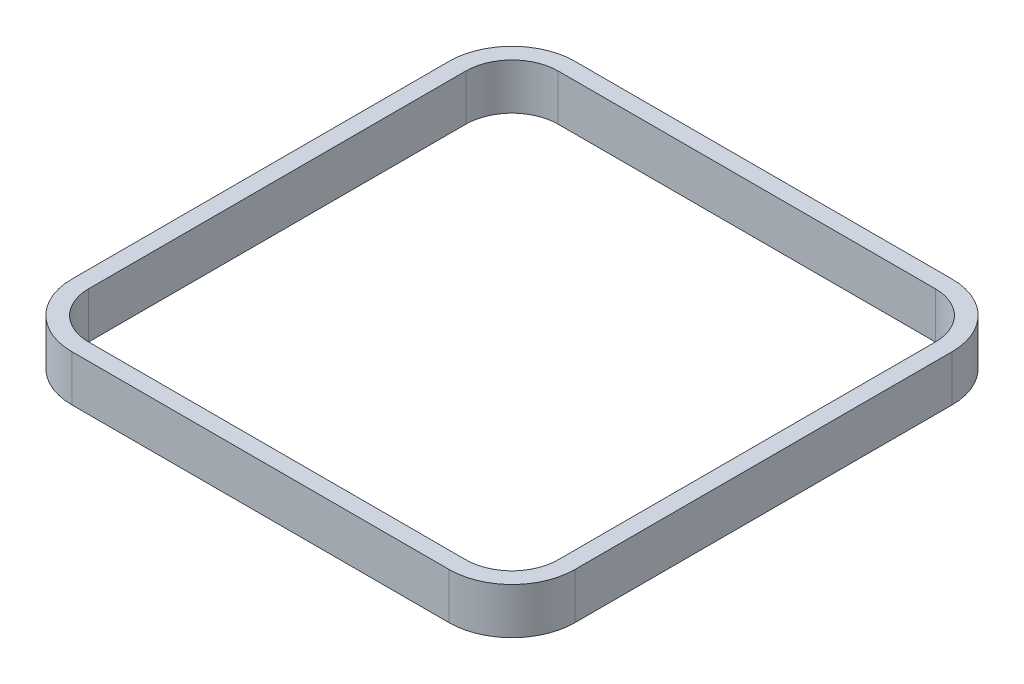
SolidWorks part; units mm, degrees
ref_plane "Front Plane" through (0, 0, 0) normal (0, 0, 1) x (1, 0, 0)
ref_plane "Top Plane" through (0, 0, 0) normal (0, 1, 0) x (1, 0, 0)
ref_plane "Right Plane" through (0, 0, 0) normal (1, 0, 0) x (0, 0, -1)
sketch "Sketch1" plane through (0, 0, 0) normal (0, 1, 0) x (1, 0, 0)
  line L1 (-450, -600) -> (450, -600)
  line L2 (-600, -450) -> (-600, 450)
  line L3 (-450, 600) -> (450, 600)
  line L4 (600, -450) -> (600, 450)
  line L5 (-600, -600) -> (600, 600) construction
  line L6 (-600, 600) -> (600, -600) construction
  arc A0 (450, 600) -> (600, 450) centre (450, 450) cw
  arc A1 (600, -450) -> (450, -600) centre (450, -450) cw
  arc A2 (-450, -600) -> (-600, -450) centre (-450, -450) cw
  arc A3 (-600, 450) -> (-450, 600) centre (-450, 450) cw
  point P0 (0, 0)
  dimension "D3" = 150
  dimension "D1" = 1200
  dimension "D2" = 1200
extrude "Boss-Extrude1" add sketch "Sketch1" along normal blind 150
sketch "Sketch2" plane through (0, 150, 0) normal (0, 1, 0) x (1, 0, 0)
  line L8 (450, 560) -> (-450, 560)
  line L9 (-560, 450) -> (-560, -450)
  line L10 (-450, -560) -> (450, -560)
  line L11 (560, -450) -> (560, 450)
  line L12 (450, 560) -> (-450, 560)
  line L13 (-560, 450) -> (-560, -450)
  line L14 (-450, -560) -> (450, -560)
  line L15 (560, -450) -> (560, 450)
  arc A8 (560, 450) -> (450, 560) centre (450, 450) ccw
  arc A9 (-450, 560) -> (-560, 450) centre (-450, 450) ccw
  arc A10 (-560, -450) -> (-450, -560) centre (-450, -450) ccw
  arc A11 (450, -560) -> (560, -450) centre (450, -450) ccw
  arc A12 (560, 450) -> (450, 560) centre (450, 450) ccw
  arc A13 (-450, 560) -> (-560, 450) centre (-450, 450) ccw
  arc A14 (-560, -450) -> (-450, -560) centre (-450, -450) ccw
  arc A15 (450, -560) -> (560, -450) centre (450, -450) ccw
  dimension "D1" = 40
extrude "Cut-Extrude1" cut sketch "Sketch2" against normal blind 110
sketch "Sketch3" plane through (0, 40, 0) normal (0, 1, 0) x (1, 0, 0)
  circle A0 centre (249.3488, 217.5584) radius 52.0745
extrude "Cut-Extrude2" cut sketch "Sketch3" against normal blind 110
sketch "Sketch4" plane through (0, 40, 0) normal (0, 1, 0) x (1, 0, 0)
  line L0 (450, 600) -> (-450, 600) construction
  line L1 (-600, 450) -> (-600, -450) construction
  circle A0 centre (-450, 450) radius 90
  circle A1 centre (450, 450) radius 90
  circle A2 centre (450, -450) radius 90
  circle A3 centre (-450, -450) radius 90
  dimension "D1" = 180
  dimension "D2" = 150
  dimension "D3" = 150
  dimension "D4" = 180
  dimension "D5" = 180
  dimension "D6" = 180
sketch "Sketch5" plane through (0, 40, 0) normal (0, 1, 0) x (1, 0, 0)
  circle A0 centre (0, 0) radius 472.5
  dimension "D1" = 945
sketch "Sketch7" plane through (0, 0, 0) normal (0, -1, 0) x (1, 0, 0)
  line L8 (600, -450) -> (600, 450)
  line L9 (450, 600) -> (-450, 600)
  line L10 (-600, 450) -> (-600, -450)
  line L11 (-450, -600) -> (450, -600)
  line L12 (600, -450) -> (600, 450)
  line L13 (450, 600) -> (-450, 600)
  line L14 (-600, 450) -> (-600, -450)
  line L15 (-450, -600) -> (450, -600)
  arc A8 (450, -600) -> (600, -450) centre (450, -450) ccw
  arc A9 (600, 450) -> (450, 600) centre (450, 450) ccw
  arc A10 (-450, 600) -> (-600, 450) centre (-450, 450) ccw
  arc A11 (-600, -450) -> (-450, -600) centre (-450, -450) ccw
  arc A12 (450, -600) -> (600, -450) centre (450, -450) ccw
  arc A13 (600, 450) -> (450, 600) centre (450, 450) ccw
  arc A14 (-450, 600) -> (-600, 450) centre (-450, 450) ccw
  arc A15 (-600, -450) -> (-450, -600) centre (-450, -450) ccw
  dimension "D1" = 0
extrude "Cut-Extrude4" cut sketch "Sketch7" against normal up to vertex (40 mm away)
